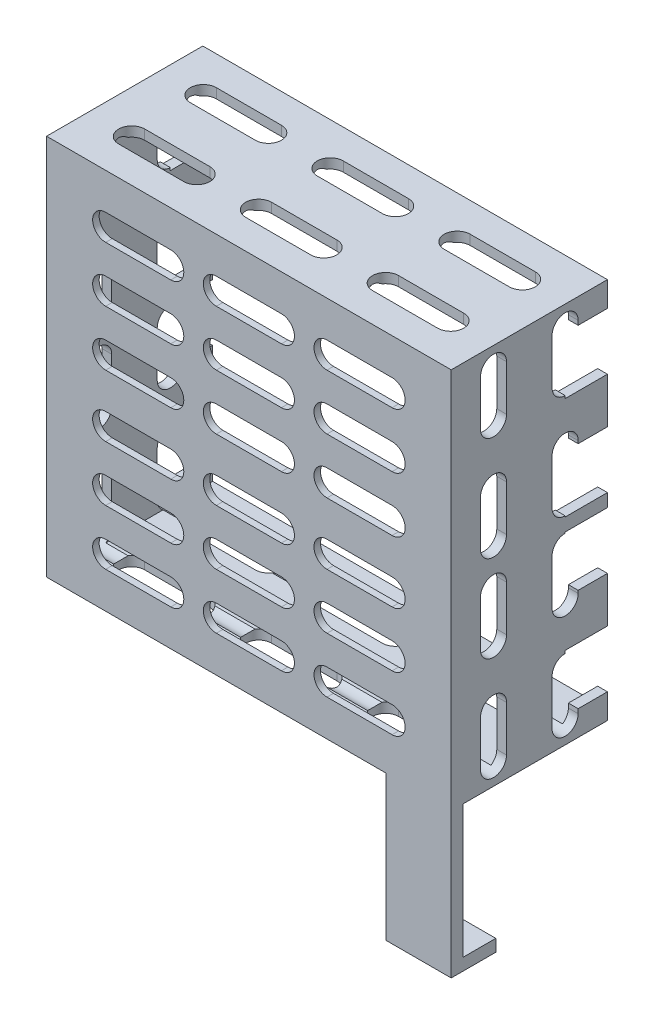
SolidWorks part; units mm, degrees
ref_plane "Front Plane" through (0, 0, 0) normal (0, 0, 1) x (1, 0, 0)
ref_plane "Top Plane" through (0, 0, 0) normal (0, 1, 0) x (1, 0, 0)
ref_plane "Right Plane" through (0, 0, 0) normal (1, 0, 0) x (0, 0, -1)
sketch "Sketch1" plane through (0, 0, 0) normal (0, 0, 1) x (1, 0, 0)
  line L4 (29.58, -14.58) -> (-29.58, -14.58)
  line L5 (29.25, -14.25) -> (-29.25, -14.25) construction
  line L6 (29.25, -14.25) -> (29.25, 14.25) construction
  line L7 (29.25, 14.25) -> (-29.25, 14.25) construction
  line L16 (-29.25, -14.25) -> (-29.25, 14.25) construction
  line L17 (-29.58, -14.58) -> (-29.58, 14.58)
  line L18 (29.58, 14.58) -> (-29.58, 14.58)
  line L19 (29.58, -14.58) -> (29.58, 14.58)
  line L20 (-31.08, -16.08) -> (-31.08, 16.08)
  line L21 (31.08, 16.08) -> (-31.08, 16.08)
  line L22 (31.08, -16.08) -> (31.08, 16.08)
  line L23 (31.08, -16.08) -> (-31.08, -16.08)
  line L24 (-29.58, -13.25) -> (-31.08, -13.25)
  line L25 (-29.25, -14.25) -> (-29.25, -12.25) construction
  line L26 (29.58, -13.25) -> (31.08, -13.25)
  point P16 (-29.25, -13.25)
  dimension "D1" = 0.33
  dimension "D2" = 1.5
extrude "Boss-Extrude1" add sketch "Sketch1" along normal blind 18 contours L19 L26 L22 L21 L20 L24 L17 L18
sketch "Sketch2" plane through (0, 0, 18) normal (0, 0, 1) x (1, 0, 0)
  line L1 (-31.08, 16.08) -> (31.08, 16.08)
  line L2 (-31.08, 16.08) -> (-31.08, -13.25)
  line L3 (-31.08, -13.25) -> (31.08, -13.25)
  line L14 (31.08, 16.08) -> (31.08, -13.25)
extrude "Boss-Extrude2" add sketch "Sketch2" along normal blind 1
sketch "Sketch3" plane through (0, 0, 0) normal (0, 0, -1) x (-1, 0, 0)
  line L40 (-29.58, -13.25) -> (-29.58, 14.58)
  line L41 (-29.58, 14.58) -> (29.58, 14.58)
  line L42 (29.58, 14.58) -> (29.58, -13.25)
  line L43 (29.58, -13.25) -> (31.08, -13.25)
  line L44 (31.08, -13.25) -> (31.08, 16.08)
  line L45 (31.08, 16.08) -> (-31.08, 16.08)
  line L46 (-31.08, 16.08) -> (-31.08, -13.25)
  line L47 (-31.08, -13.25) -> (-29.58, -13.25)
  line L48 (-29.58, -13.25) -> (-29.58, 14.58)
  line L49 (-29.58, 14.58) -> (29.58, 14.58)
  line L50 (29.58, 14.58) -> (29.58, -13.25)
  line L51 (29.58, -13.25) -> (31.08, -13.25)
  line L52 (31.08, -13.25) -> (31.08, 16.08)
  line L53 (31.08, 16.08) -> (-31.08, 16.08)
  line L54 (-31.08, 16.08) -> (-31.08, -13.25)
  line L55 (-31.08, -13.25) -> (-29.58, -13.25)
  dimension "D1" = 0
extrude "Boss-Extrude3" add sketch "Sketch3" along normal up to surface (5 mm away)
sketch "Sketch8" plane through (0, 0, 18) normal (0, 0, -1) x (-1, 0, 0)
  line L0 (12, 6.5) -> (22, 6.5) construction
  line L1 (12, -2) -> (22, -2) construction
  line L2 (12, -10.5) -> (22, -10.5) construction
  line L3 (-5, -10.5) -> (5, -10.5) construction
  line L4 (-22, -10.5) -> (-12, -10.5) construction
  line L5 (-22, -2) -> (-12, -2) construction
  line L6 (-5, 6.5) -> (5, 6.5) construction
  line L7 (-22, 6.5) -> (-12, 6.5) construction
  line L8 (12, 6.5) -> (22, 6.5)
  line L9 (12, -2) -> (22, -2)
  line L10 (12, -10.5) -> (22, -10.5)
  line L11 (-5, -10.5) -> (5, -10.5)
  line L12 (-22, -10.5) -> (-12, -10.5)
  line L13 (-22, -2) -> (-12, -2)
  line L14 (-5, 6.5) -> (5, 6.5)
  line L15 (-22, 6.5) -> (-12, 6.5)
  line L16 (22, -6.5) -> (12, -6.5) construction
  line L17 (5, -6.5) -> (-5, -6.5) construction
  line L18 (-12, -6.5) -> (-22, -6.5) construction
  line L19 (22, 2) -> (12, 2) construction
  line L20 (-5, -2) -> (5, -2) construction
  line L21 (5, 2) -> (-5, 2) construction
  line L22 (-12, 2) -> (-22, 2) construction
  line L23 (22, 10.5) -> (12, 10.5) construction
  line L24 (5, 10.5) -> (-5, 10.5) construction
  line L25 (-12, 10.5) -> (-22, 10.5) construction
  line L26 (22, -6.5) -> (12, -6.5)
  line L27 (5, -6.5) -> (-5, -6.5)
  line L28 (-12, -6.5) -> (-22, -6.5)
  line L29 (22, 2) -> (12, 2)
  line L30 (-5, -2) -> (5, -2)
  line L31 (5, 2) -> (-5, 2)
  line L32 (-12, 2) -> (-22, 2)
  line L33 (22, 10.5) -> (12, 10.5)
  line L34 (5, 10.5) -> (-5, 10.5)
  line L35 (-12, 10.5) -> (-22, 10.5)
  arc A0 (22, -10.5) -> (22, -6.5) centre (22, -8.5) ccw construction
  arc A1 (12, -6.5) -> (12, -10.5) centre (12, -8.5) ccw construction
  arc A2 (5, -10.5) -> (5, -6.5) centre (5, -8.5) ccw construction
  arc A3 (-5, -6.5) -> (-5, -10.5) centre (-5, -8.5) ccw construction
  arc A4 (-12, -10.5) -> (-12, -6.5) centre (-12, -8.5) ccw construction
  arc A5 (-22, -6.5) -> (-22, -10.5) centre (-22, -8.5) ccw construction
  arc A6 (22, -2) -> (22, 2) centre (22, 0) ccw construction
  arc A7 (12, 2) -> (12, -2) centre (12, 0) ccw construction
  arc A8 (-5, 2) -> (-5, -2) centre (-5, 0) ccw construction
  arc A9 (5, -2) -> (5, 2) centre (5, 0) ccw construction
  arc A10 (-12, -2) -> (-12, 2) centre (-12, 0) ccw construction
  arc A11 (-22, 2) -> (-22, -2) centre (-22, 0) ccw construction
  arc A12 (22, 6.5) -> (22, 10.5) centre (22, 8.5) ccw construction
  arc A13 (12, 10.5) -> (12, 6.5) centre (12, 8.5) ccw construction
  arc A14 (-5, 10.5) -> (-5, 6.5) centre (-5, 8.5) ccw construction
  arc A15 (-12, 6.5) -> (-12, 10.5) centre (-12, 8.5) ccw construction
  arc A16 (-22, 10.5) -> (-22, 6.5) centre (-22, 8.5) ccw construction
  arc A17 (22, -10.5) -> (22, -6.5) centre (22, -8.5) ccw
  arc A18 (12, -6.5) -> (12, -10.5) centre (12, -8.5) ccw
  arc A19 (5, -10.5) -> (5, -6.5) centre (5, -8.5) ccw
  arc A20 (-5, -6.5) -> (-5, -10.5) centre (-5, -8.5) ccw
  arc A21 (-12, -10.5) -> (-12, -6.5) centre (-12, -8.5) ccw
  arc A22 (-22, -6.5) -> (-22, -10.5) centre (-22, -8.5) ccw
  arc A23 (22, -2) -> (22, 2) centre (22, 0) ccw
  arc A24 (12, 2) -> (12, -2) centre (12, 0) ccw
  arc A25 (-5, 2) -> (-5, -2) centre (-5, 0) ccw
  arc A26 (5, -2) -> (5, 2) centre (5, 0) ccw
  arc A27 (-12, -2) -> (-12, 2) centre (-12, 0) ccw
  arc A28 (-22, 2) -> (-22, -2) centre (-22, 0) ccw
  arc A29 (22, 6.5) -> (22, 10.5) centre (22, 8.5) ccw
  arc A30 (12, 10.5) -> (12, 6.5) centre (12, 8.5) ccw
  arc A31 (-5, 10.5) -> (-5, 6.5) centre (-5, 8.5) ccw
  arc A32 (-12, 6.5) -> (-12, 10.5) centre (-12, 8.5) ccw
  arc A33 (-22, 10.5) -> (-22, 6.5) centre (-22, 8.5) ccw
  arc A34 (5, 6.5) -> (5, 10.5) centre (5, 8.5) ccw construction
  arc A35 (5, 6.5) -> (5, 10.5) centre (5, 8.5) ccw
extrude "Cut-Extrude4" cut sketch "Sketch8" against normal through all
sketch "Sketch5" plane through (-15, 16.08, 0) normal (0, -1, 0) x (1, 0, 0)
  line L0 (-9.5, 1.5) -> (0.5, 1.5) construction
  line L1 (-9.5, 3.5) -> (0.5, 3.5)
  line L2 (-9.5, -0.5) -> (0.5, -0.5)
  line L3 (-16.08, 7) -> (46.08, 7) construction
  line L4 (46.08, 19) -> (46.08, -5) construction
  line L5 (-15.85, 19) -> (45.85, 19) construction
  line L6 (15, -5) -> (15, 19) construction
  line L7 (46.08, 12.5) -> (-16.08, 12.5) construction
  line L9 (-4.5, 19) -> (-4.5, -5) construction
  line L10 (46.08, 1.5) -> (-16.08, 1.5) construction
  line L11 (34.5, 19) -> (34.5, -5) construction
  line L12 (44.58, -5) -> (-14.58, -5) construction
  line L13 (10, -0.5) -> (20, -0.5)
  line L14 (10, 3.5) -> (20, 3.5)
  line L15 (10, 1.5) -> (20, 1.5) construction
  line L16 (29.5, -0.5) -> (39.5, -0.5)
  line L17 (29.5, 3.5) -> (39.5, 3.5)
  line L18 (29.5, 1.5) -> (39.5, 1.5) construction
  line L19 (10, 10.5) -> (20, 10.5)
  line L20 (10, 14.5) -> (20, 14.5)
  line L21 (10, 12.5) -> (20, 12.5) construction
  line L22 (29.5, 10.5) -> (39.5, 10.5)
  line L23 (29.5, 14.5) -> (39.5, 14.5)
  line L24 (29.5, 12.5) -> (39.5, 12.5) construction
  line L25 (-9.5, 10.5) -> (0.5, 10.5)
  line L26 (-9.5, 14.5) -> (0.5, 14.5)
  line L27 (-9.5, 12.5) -> (0.5, 12.5) construction
  line L29 (-16.08, 19) -> (46.08, 19) construction
  line L30 (-16.08, 19) -> (-16.08, -5) construction
  arc A0 (-9.5, 3.5) -> (-9.5, -0.5) centre (-9.5, 1.5) ccw
  arc A1 (0.5, -0.5) -> (0.5, 3.5) centre (0.5, 1.5) ccw
  arc A2 (10, 3.5) -> (10, -0.5) centre (10, 1.5) ccw
  arc A3 (20, -0.5) -> (20, 3.5) centre (20, 1.5) ccw
  arc A4 (29.5, 3.5) -> (29.5, -0.5) centre (29.5, 1.5) ccw
  arc A5 (39.5, -0.5) -> (39.5, 3.5) centre (39.5, 1.5) ccw
  arc A6 (10, 14.5) -> (10, 10.5) centre (10, 12.5) ccw
  arc A7 (20, 10.5) -> (20, 14.5) centre (20, 12.5) ccw
  arc A8 (29.5, 14.5) -> (29.5, 10.5) centre (29.5, 12.5) ccw
  arc A9 (39.5, 10.5) -> (39.5, 14.5) centre (39.5, 12.5) ccw
  arc A10 (-9.5, 14.5) -> (-9.5, 10.5) centre (-9.5, 12.5) ccw
  arc A11 (0.5, 10.5) -> (0.5, 14.5) centre (0.5, 12.5) ccw
  point P2 (-4.5, 1.5)
  point P12 (46.08, 7)
  point P21 (15, -5)
  point P29 (15, 19)
  point P31 (15, 1.5)
  point P38 (34.5, 1.5)
  point P45 (15, 12.5)
  point P52 (34.5, 12.5)
  point P59 (-4.5, 12.5)
  dimension "D1" = 10
  dimension "D2" = 4
  dimension "D3" = 39
  dimension "D4" = 11
  dimension "D5" = 3
  dimension "D6" = 2
extrude "Cut-Extrude2" cut sketch "Sketch5" along normal through all
sketch "Sketch7" plane through (31.08, -15, 0) normal (-1, 0, 0) x (0, 0, -1)
  line L0 (-12.5, -27.915) -> (-12.5, -20.915) construction
  line L1 (-14.5, -27.915) -> (-14.5, -20.915)
  line L2 (-10.5, -27.915) -> (-10.5, -20.915)
  line L3 (-19, -16.415) -> (5, -16.415) construction
  line L6 (-7, 0.85) -> (-7, -31.08) construction
  line L7 (-19, 0.85) -> (5, 0.85) construction
  line L8 (-19, -31.08) -> (5, -31.08) construction
  line L9 (-12.5, -31.08) -> (-12.5, 0.85) construction
  line L10 (-19, -8.415) -> (5, -8.415) construction
  line L11 (-19, -24.415) -> (5, -24.415) construction
  line L12 (-1.5, -31.08) -> (-1.5, 0.85) construction
  line L13 (0.5, -27.915) -> (0.5, -20.915)
  line L14 (-3.5, -27.915) -> (-3.5, -20.915)
  line L15 (-1.5, -27.915) -> (-1.5, -20.915) construction
  line L16 (0.5, -11.915) -> (0.5, -4.915)
  line L17 (-3.5, -11.915) -> (-3.5, -4.915)
  line L18 (-1.5, -11.915) -> (-1.5, -4.915) construction
  line L19 (-10.5, -11.915) -> (-10.5, -4.915)
  line L20 (-14.5, -11.915) -> (-14.5, -4.915)
  line L21 (-12.5, -11.915) -> (-12.5, -4.915) construction
  line L22 (-19, -31.08) -> (-19, -1.75) construction
  line L23 (5, -1.75) -> (5, -31.08) construction
  arc A0 (-14.5, -27.915) -> (-10.5, -27.915) centre (-12.5, -27.915) ccw
  arc A1 (-10.5, -20.915) -> (-14.5, -20.915) centre (-12.5, -20.915) ccw
  arc A2 (-3.5, -27.915) -> (0.5, -27.915) centre (-1.5, -27.915) ccw
  arc A3 (0.5, -20.915) -> (-3.5, -20.915) centre (-1.5, -20.915) ccw
  arc A4 (-3.5, -11.915) -> (0.5, -11.915) centre (-1.5, -11.915) ccw
  arc A5 (0.5, -4.915) -> (-3.5, -4.915) centre (-1.5, -4.915) ccw
  arc A6 (-14.5, -11.915) -> (-10.5, -11.915) centre (-12.5, -11.915) ccw
  arc A7 (-10.5, -4.915) -> (-14.5, -4.915) centre (-12.5, -4.915) ccw
  point P2 (-12.5, -24.415)
  point P16 (-19, -16.415)
  point P32 (-1.5, -24.415)
  point P39 (-1.5, -8.415)
  point P46 (-12.5, -8.415)
  dimension "D1" = 7
  dimension "D2" = 4
  dimension "D3" = 16
  dimension "D6" = 11
  dimension "D4" = 2
  dimension "D5" = 2
extrude "Cut-Extrude3" cut sketch "Sketch7" along normal through all
sketch "Sketch9" plane through (-31.08, 0, 0) normal (-1, 0, 0) x (0, 0, 1)
  line L0 (-5, 0) -> (19, 0) construction
  line L1 (-5, 3.5) -> (1.5, 3.5)
  line L2 (-5, 3.5) -> (-5, 12.25)
  line L3 (-5, 12.25) -> (1.5, 12.25)
  line L4 (1.5, 3.5) -> (1.5, 12.25)
  line L6 (-5, -15.85) -> (-5, 15.85) construction
  line L7 (19, 15.85) -> (19, -15.85) construction
  line L8 (1.5, -3.5) -> (1.5, -12.25)
  line L9 (-5, -12.25) -> (1.5, -12.25)
  line L10 (-5, -3.5) -> (-5, -12.25)
  line L11 (-5, -3.5) -> (1.5, -3.5)
  arc A0 (3.5, 12.915) -> (-0.5, 12.915) centre (1.5, 12.915) ccw construction
  point P22 (1.5, 14.915)
extrude "Cut-Extrude5" cut sketch "Sketch9" against normal through all
mirror "Mirror1" about plane through (0, -13.25, 18) normal (0, -1, 0) of bodies 108
sketch "Sketch10" plane through (31.08, 0, 0) normal (1, 0, 0) x (0, 0, -1)
  line L0 (-19, -42.58) -> (-19, -64.83)
  line L1 (-19, -64.83) -> (-12.15, -64.83)
  line L2 (-12.15, -64.83) -> (-12.15, -62.98)
  line L3 (-12.15, -62.98) -> (-17.15, -62.98)
  line L4 (-17.15, -62.98) -> (-17.15, -42.58)
  line L5 (-19, -42.58) -> (5, -42.58) construction
  line L6 (-17.15, -42.58) -> (-19, -42.58)
  line L7 (-16.95, -42.78) -> (-16.95, -62.78) construction
  line L8 (-16.95, -62.78) -> (-0.95, -62.78) construction
  dimension "D1" = 0.2
  dimension "D2" = 0.2
  dimension "D3" = 5
extrude "Boss-Extrude4" add sketch "Sketch10" against normal blind 10
